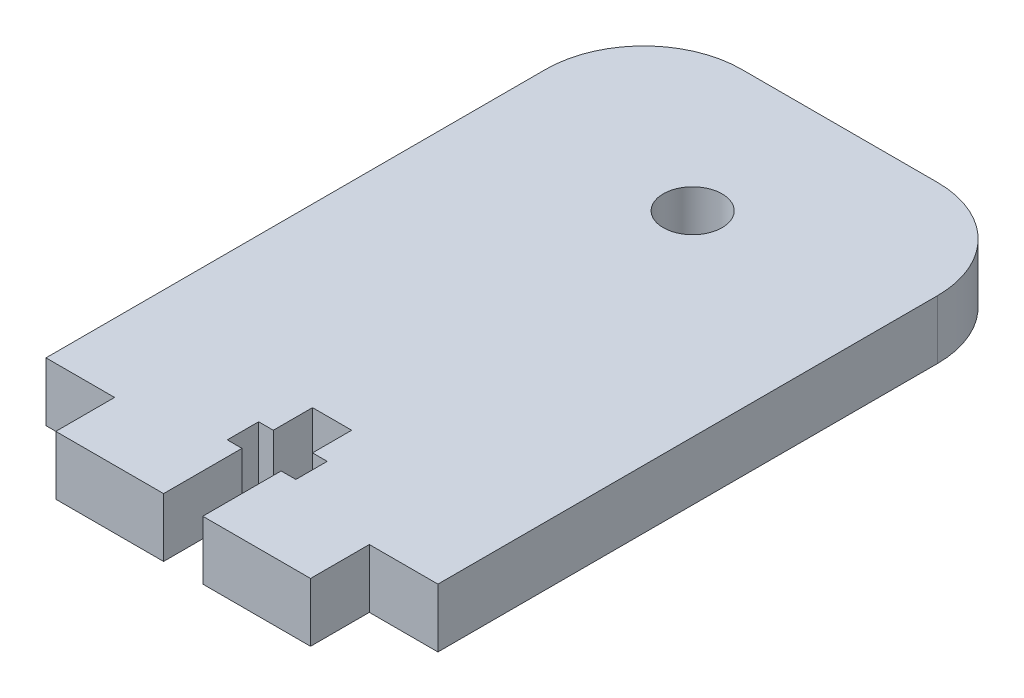
SolidWorks part; units mm, degrees
ref_plane "Front Plane" through (0, 0, 0) normal (0, 0, 1) x (1, 0, 0)
ref_plane "Top Plane" through (0, 0, 0) normal (0, 1, 0) x (1, 0, 0)
ref_plane "Right Plane" through (0, 0, 0) normal (1, 0, 0) x (0, 0, -1)
sketch "Sketch1" plane through (0, 0, 0) normal (0, 1, 0) x (1, 0, 0)
  line L0 (-12.7618, -32.5471) -> (-1.7618, -32.5471) construction
  line L1 (-9.7618, 34.4529) -> (10.2382, 34.4529)
  line L2 (-1.7618, -32.5471) -> (-1.7618, -24.5471)
  line L3 (-1.7618, -24.5471) -> (-3.2618, -24.5471)
  line L4 (0.2382, 34.4529) -> (0.2382, 19.4529) construction
  line L5 (-3.2618, -24.5471) -> (-3.2618, -21.3471)
  line L6 (-12.7618, -26.5471) -> (-19.7618, -26.5471)
  line L7 (13.2382, -26.5471) -> (20.2382, -26.5471)
  line L8 (-19.7618, 24.4529) -> (-19.7618, -26.5471)
  line L9 (20.2382, 24.4529) -> (20.2382, -26.5471)
  line L10 (-3.2618, -21.3471) -> (-1.7618, -21.3471)
  line L11 (-1.7618, -21.3471) -> (-1.7618, -17.3471)
  line L12 (-12.7618, -26.5471) -> (-12.7618, -32.5471)
  line L13 (-12.7618, -32.5471) -> (-1.7618, -32.5471)
  line L14 (13.2382, -26.5471) -> (13.2382, -32.5471)
  line L15 (-1.7618, -17.3471) -> (2.2382, -17.3471)
  line L16 (2.2382, -17.3471) -> (2.2382, -21.3471)
  line L17 (2.2382, -21.3471) -> (3.7382, -21.3471)
  line L18 (3.7382, -21.3471) -> (3.7382, -24.5471)
  line L19 (3.7382, -24.5471) -> (2.2382, -24.5471)
  line L20 (2.2382, -24.5471) -> (2.2382, -32.5471)
  line L21 (2.2382, -32.5471) -> (13.2382, -32.5471)
  arc A0 (10.2382, 34.4529) -> (20.2382, 24.4529) centre (10.2382, 24.4529) cw
  arc A1 (-9.7618, 34.4529) -> (-19.7618, 24.4529) centre (-9.7618, 24.4529) ccw
  circle A2 centre (0.2382, 19.4529) radius 3
  point P0 (0.2382, -25.5471)
  dimension "D2" = 6
  dimension "D3" = 10
  dimension "D1" = 15
  dimension "D4" = 61
  dimension "D5" = 40
  dimension "D6" = 7
  dimension "D7" = 7
  dimension "D8" = 26
  dimension "D9" = 6
  dimension "D10" = 4
  dimension "D11" = 11
  dimension "D12" = 8
  dimension "D13" = 1.5
  dimension "D14" = 3.2
  dimension "D15" = 1.5
  dimension "D16" = 4
extrude "Boss-Extrude1" add sketch "Sketch1" along normal blind 6
